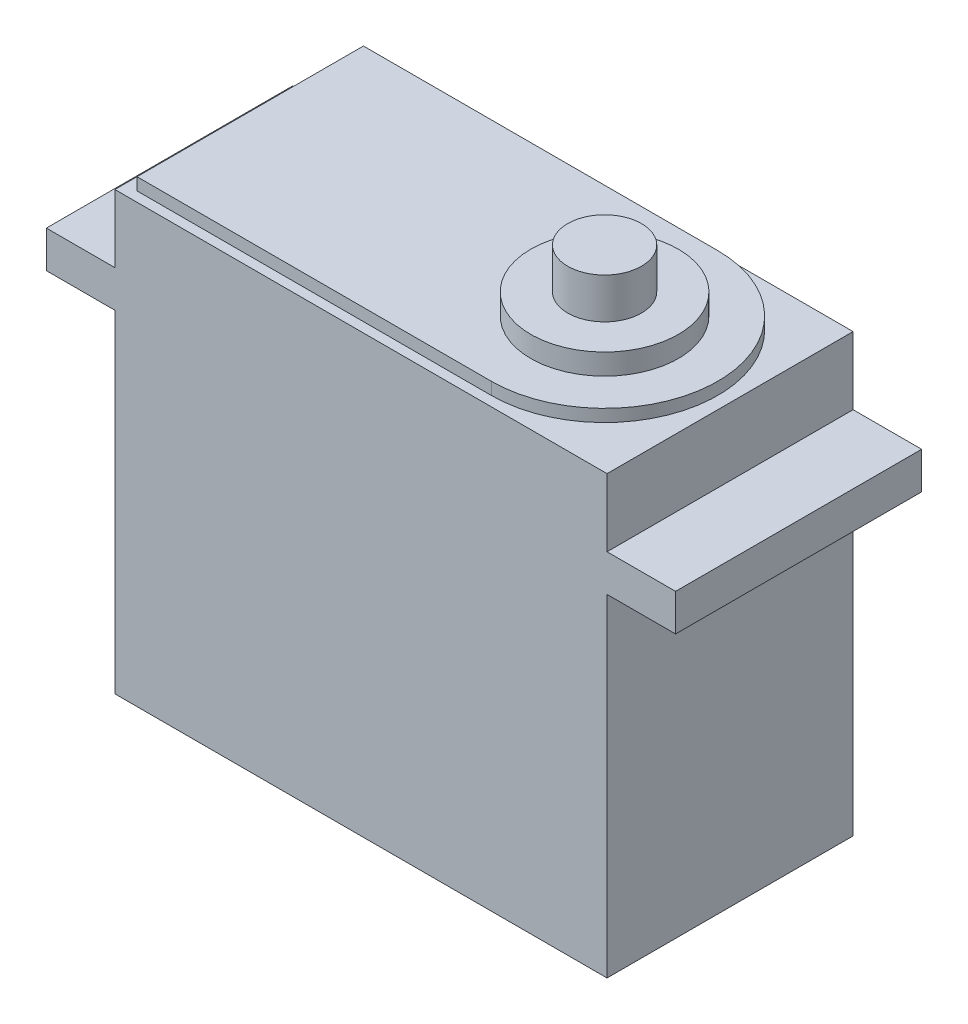
SolidWorks part; units mm, degrees
material "ABS"
ref_plane "Plano frontal" through (0, 0, 0) normal (0, 0, 1) x (1, 0, 0)
ref_plane "Plano superior" through (0, 0, 0) normal (0, 1, 0) x (1, 0, 0)
ref_plane "Plano direito" through (0, 0, 0) normal (1, 0, 0) x (0, 0, -1)
sketch "Esboço1" plane through (0, 0, 0) normal (0, 0, 1) x (1, 0, 0)
  line L0 (20, -0.7679) -> (25.5689, -0.7679)
  line L1 (25.5689, -0.7679) -> (25.5689, -3.7679)
  line L2 (25.5689, -3.7679) -> (20, -3.7679)
  line L3 (20, -3.7679) -> (20, -30.7679)
  line L4 (20, -30.7679) -> (-20, -30.7679)
  line L5 (0, -30.7679) -> (0, 0) construction
  line L6 (20, -0.7679) -> (20, 4.7321)
  line L7 (20, 4.7321) -> (-20, 4.7321)
  line L8 (-20, -0.7679) -> (-20, 4.7321)
  line L9 (-20, -3.7679) -> (-20, -30.7679)
  line L10 (-25.5689, -3.7679) -> (-20, -3.7679)
  line L11 (-25.5689, -0.7679) -> (-25.5689, -3.7679)
  line L12 (-20, -0.7679) -> (-25.5689, -0.7679)
  point P11 (0, 4.7321)
  dimension "D1" = 40
  dimension "D2" = 27
  dimension "D3" = 3
  dimension "D4" = 5.5
extrude "Ressalto-extrusão1" add sketch "Esboço1" along normal mid plane 20
sketch "Esboço3" plane through (0, 4.7321, 0) normal (0, 1, 0) x (1, 0, 0)
  line L0 (20, -10) -> (-20, -10) construction
  line L1 (-19, 9.2) -> (9.8, 9.2)
  line L2 (-19, 9.2) -> (-19, -9.2)
  line L3 (-19, -9.2) -> (9.8, -9.2)
  arc A1 (9.8, -9.2) -> (9.8, 9.2) centre (9.8, 0) ccw
  point P0 (0, 0)
  dimension "D1" = 0.8
extrude "Ressalto-extrusão2" add sketch "Esboço3" along normal blind 1
sketch "Esboço4" plane through (0, 5.7321, 0) normal (0, 1, 0) x (1, 0, 0)
  circle A0 centre (9.8, 0) radius 3
extrude "Ressalto-extrusão3" add sketch "Esboço4" along normal blind 5
sketch "Esboço5" plane through (0, 5.7321, 0) normal (0, 1, 0) x (1, 0, 0)
  circle A0 centre (9.8, 0) radius 6
extrude "Ressalto-extrusão4" add sketch "Esboço5" along normal blind 1.7
